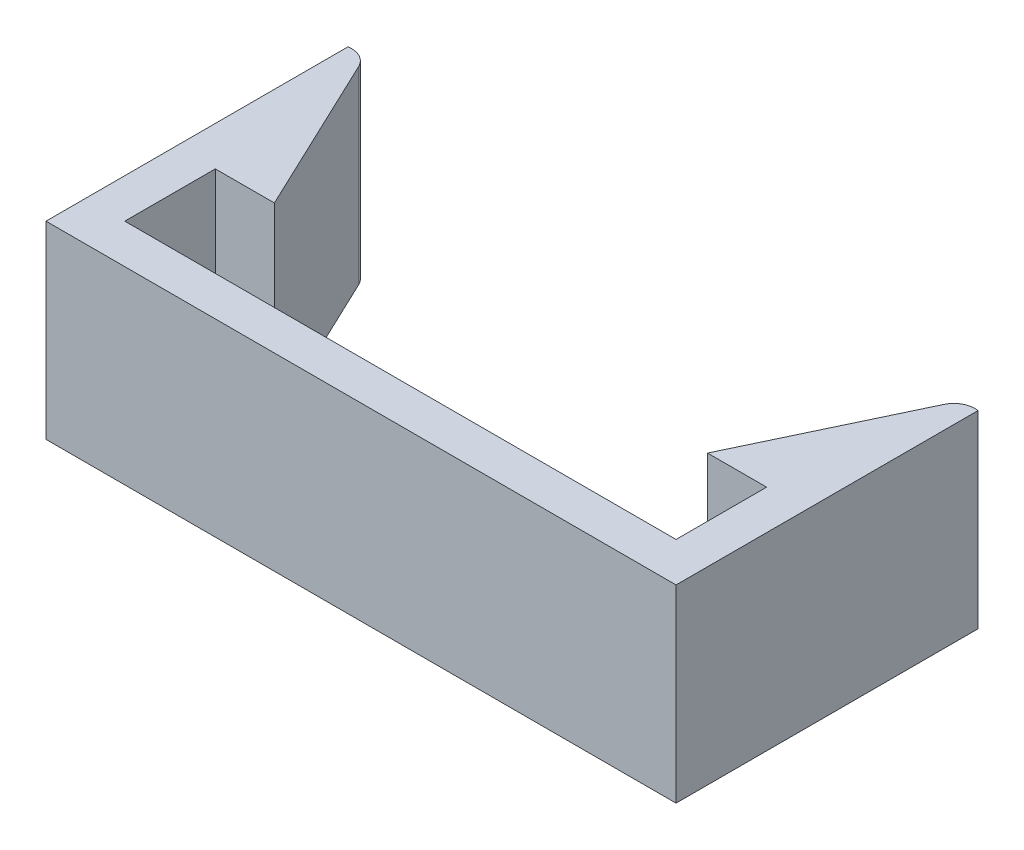
SolidWorks part; units mm, degrees
ref_plane "前基準面" through (0, 0, 0) normal (0, 0, 1) x (1, 0, 0)
ref_plane "上基準面" through (0, 0, 0) normal (0, 1, 0) x (1, 0, 0)
ref_plane "右基準面" through (0, 0, 0) normal (1, 0, 0) x (0, 0, -1)
sketch "草圖1" plane through (0, 0, 0) normal (0, 1, 0) x (1, 0, 0)
  line L0 (0, -55) -> (0, 55) construction
  line L1 (-7, 1) -> (7, 1)
  line L2 (-8, 1) -> (-8, 0)
  line L3 (-8, 0) -> (8, 0)
  line L4 (8, 1) -> (8, 0)
  line L5 (-55, 0) -> (55, 0) construction
  line L6 (-8, 1) -> (-8, 7.668)
  line L7 (-7.4311, 7.3711) -> (-5.5, 3.3)
  line L8 (-5.5, 3.3) -> (-7, 3.3)
  line L9 (-7, 3.3) -> (-7, 1)
  line L10 (7, 3.3) -> (7, 1)
  line L11 (5.5, 3.3) -> (7, 3.3)
  line L12 (7.4311, 7.3711) -> (5.5, 3.3)
  line L13 (8, 1) -> (8, 7.668)
  arc A0 (-7.4311, 7.3711) -> (-8, 7.668) centre (-7.9121, 7.1429) ccw
  arc A1 (7.4311, 7.3711) -> (8, 7.668) centre (7.9121, 7.1429) cw
  point P20 (0, 0)
  point P21 (-7.9534, 7.631)
  point P22 (0, 0)
  dimension "D1" = 16
  dimension "D3" = 1
  dimension "D4" = 1
  dimension "D5" = 1.5
  dimension "D6" = 2.3
  dimension "D7" = 1
extrude "填料-伸長1" add sketch "草圖1" along normal blind 4.8
